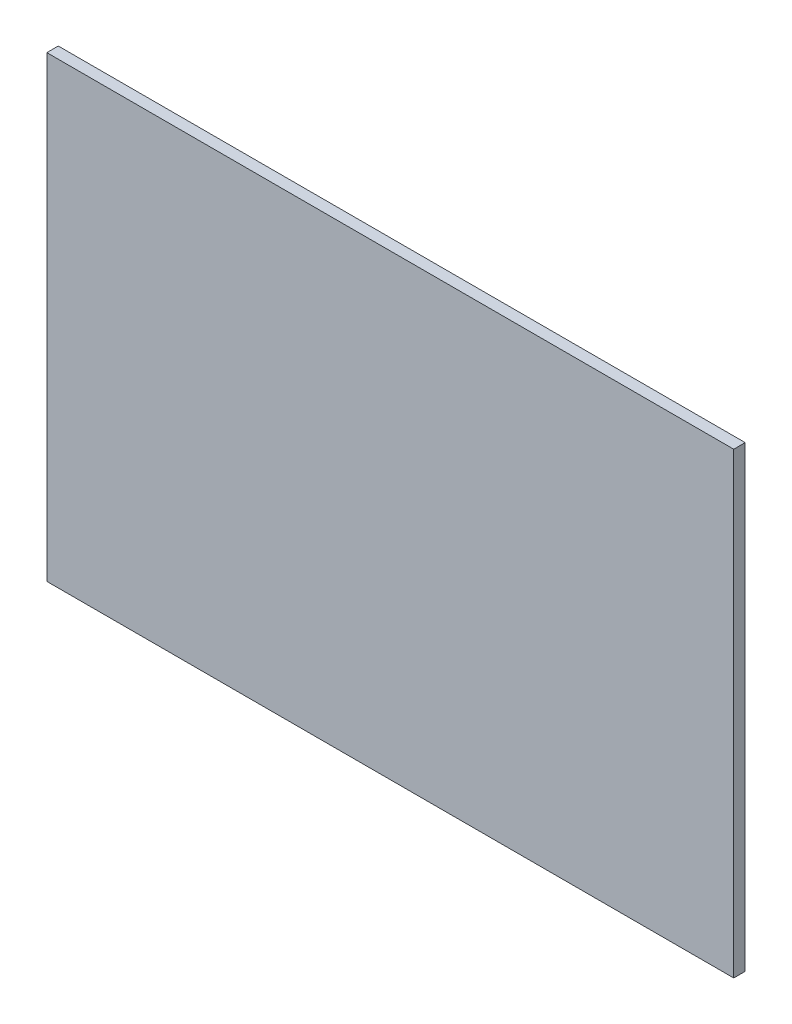
SolidWorks part; units mm, degrees
ref_plane "Plan de face" through (0, 0, 0) normal (0, 0, 1) x (1, 0, 0)
ref_plane "Plan de dessus" through (0, 0, 0) normal (0, 1, 0) x (1, 0, 0)
ref_plane "Plan de droite" through (0, 0, 0) normal (1, 0, 0) x (0, 0, -1)
sketch "Esquisse2" plane through (0, 0, 0) normal (0, 0, 1) x (1, 0, 0)
  line L1 (-67.8416, 189.7807) -> (232.1584, 189.7807)
  line L2 (-67.8416, 189.7807) -> (-67.8416, -10.2193)
  line L3 (-67.8416, -10.2193) -> (232.1584, -10.2193)
  line L4 (232.1584, 189.7807) -> (232.1584, -10.2193)
extrude "Boss.-Extru.1" add sketch "Esquisse2" along normal blind 5
